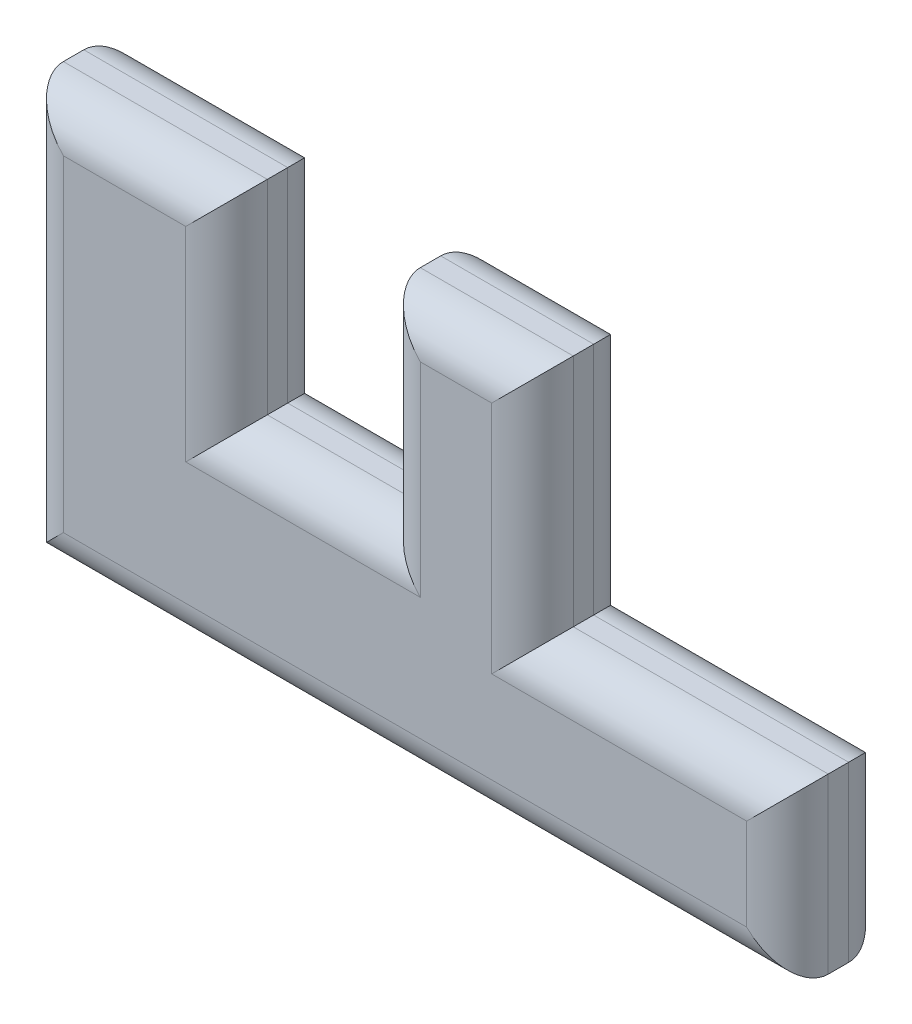
SolidWorks part; units mm, degrees
ref_plane "Front Plane" through (0, 0, 0) normal (0, 0, 1) x (1, 0, 0)
ref_plane "Top Plane" through (0, 0, 0) normal (0, 1, 0) x (1, 0, 0)
ref_plane "Right Plane" through (0, 0, 0) normal (1, 0, 0) x (0, 0, -1)
sketch "Sketch3" plane through (0, 0, 0) normal (0, 0, 1) x (1, 0, 0)
  line L0 (0, 0) -> (0, 50.8)
  line L1 (0, 50.8) -> (25.4, 50.8)
  line L2 (25.4, 50.8) -> (25.4, 25.4)
  line L3 (25.4, 25.4) -> (44.45, 25.4)
  line L4 (44.45, 25.4) -> (44.45, 50.8)
  line L5 (44.45, 50.8) -> (63.5, 50.8)
  line L6 (63.5, 50.8) -> (63.5, 21.59)
  line L7 (63.5, 21.59) -> (95.25, 21.59)
  line L8 (95.25, 21.59) -> (95.25, 0)
  line L9 (95.25, 0) -> (0, 0)
  dimension "D1" = 95.25
  dimension "D2" = 50.8
  dimension "D3" = 25.4
  dimension "D4" = 44.45
  dimension "D5" = 63.5
  dimension "D6" = 21.59
  dimension "D7" = 25.4
extrude "Boss-Extrude1" add sketch "Sketch3" along normal blind 12.7
fillet "Fillet1" radius 5.08 20 edges at (95.25, 10.795, 0) (79.375, 21.59, 0) (63.5, 36.195, 0) (53.975, 50.8, 0) (44.45, 38.1, 0) (34.925, 25.4, 0) (25.4, 38.1, 0) (12.7, 50.8, 0) (0, 25.4, 0) (47.625, 0, 0) (0, 25.4, 12.7) (12.7, 50.8, 12.7) (25.4, 38.1, 12.7) (34.925, 25.4, 12.7) (44.45, 38.1, 12.7) (53.975, 50.8, 12.7) (63.5, 36.195, 12.7) (79.375, 21.59, 12.7) (95.25, 10.795, 12.7) (47.625, 0, 12.7)
